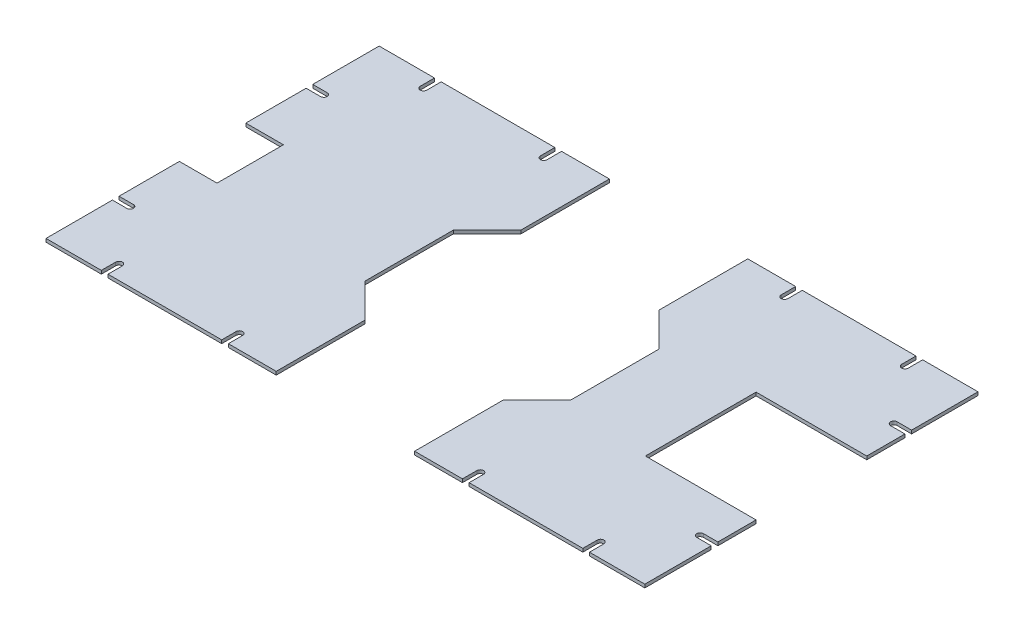
SolidWorks part; units mm, degrees
ref_plane "Front Plane" through (0, 0, 0) normal (0, 0, 1) x (1, 0, 0)
ref_plane "Top Plane" through (0, 0, 0) normal (0, 1, 0) x (1, 0, 0)
ref_plane "Right Plane" through (0, 0, 0) normal (1, 0, 0) x (0, 0, -1)
sketch "Sketch1" plane through (0, 0, 0) normal (0, 1, 0) x (1, 0, 0)
  line L1 (-270.5, -150.5) -> (270.5, -150.5)
  line L2 (-270.5, -150.5) -> (-270.5, 150.5)
  line L3 (-270.5, 150.5) -> (270.5, 150.5)
  line L4 (270.5, -150.5) -> (270.5, 150.5)
  line L5 (-270.5, -150.5) -> (270.5, 150.5) construction
  line L6 (-270.5, 150.5) -> (270.5, -150.5) construction
  point P0 (0, 0)
  dimension "D1" = 301
  dimension "D2" = 541
extrude "Boss-Extrude1" add sketch "Sketch1" along normal blind 3
sketch "Sketch2" plane through (0, 0, 0) normal (0, -1, 0) x (1, 0, 0)
  line L0 (0, 0) -> (-439.178, 0) construction
  line L1 (-236.5, -30) -> (-236.5, 30)
  line L2 (-236.5, 30) -> (-270.5, 30)
  line L3 (-270.5, -150.5) -> (-270.5, 150.5) construction
  line L4 (-236.5, -30) -> (-270.5, -30)
  line L5 (-270.5, -30) -> (-270.5, 30)
  point P9 (-236.5, 0)
  dimension "D1" = 30
  dimension "D2" = 34
extrude "Cut-Extrude1" cut sketch "Sketch2" against normal blind 10 contours L2 L5 L4 L1
sketch "Sketch3" plane through (0, 0, 0) normal (0, -1, 0) x (1, 0, 0)
  line L0 (270.5, 0) -> (126.2632, 0) construction
  line L2 (370.5, -50) -> (170.5, -50)
  line L3 (370.5, -50) -> (370.5, 50)
  line L4 (370.5, 50) -> (170.5, 50)
  line L5 (170.5, -50) -> (170.5, 50)
  line L6 (370.5, -50) -> (170.5, 50) construction
  line L7 (370.5, 50) -> (170.5, -50) construction
  dimension "D1" = 200
  dimension "D2" = 100
extrude "Cut-Extrude2" cut sketch "Sketch3" against normal blind 5
sketch "Sketch4" plane through (0, 3, 0) normal (0, 1, 0) x (1, 0, 0)
  line L0 (270.5, 150.5) -> (-270.5, 150.5) construction
  line L1 (-62.5, -150.5) -> (62.5, -150.5)
  line L2 (-62.5, -150.5) -> (-62.5, 150.5)
  line L3 (-62.5, 150.5) -> (62.5, 150.5)
  line L4 (62.5, -150.5) -> (62.5, 150.5)
  line L5 (-62.5, -150.5) -> (62.5, 150.5) construction
  line L6 (-62.5, 150.5) -> (62.5, -150.5) construction
  point P0 (0, 0)
  dimension "D1" = 125
extrude "Cut-Extrude3" cut sketch "Sketch4" against normal blind 5
sketch "Sketch5" plane through (0, 3, 0) normal (0, 1, 0) x (1, 0, 0)
  line L0 (0, 0) -> (270.5, 0) construction
  line L1 (270.5, 0) -> (0, 0) construction
  line L2 (0, -150.5) -> (0, 150.5) construction
  line L6 (270.5, 50) -> (270.5, 150.5) construction
  line L7 (-220.5, 150.5) -> (-220.5, 137.5)
  line L8 (-62.5, 150.5) -> (-270.5, 150.5) construction
  line L9 (-214.5, 137.5) -> (-214.5, 150.5)
  line L10 (-214.5, 150.5) -> (-220.5, 150.5)
  line L11 (-270.5, 150.5) -> (-270.5, 30) construction
  line L12 (-105.75, 137.5) -> (-105.75, 150.5)
  line L13 (-111.75, 150.5) -> (-111.75, 137.5)
  line L14 (-105.75, 150.5) -> (-111.75, 150.5)
  line L15 (3, 137.5) -> (3, 150.5)
  line L16 (-3, 150.5) -> (-3, 137.5)
  line L17 (3, 150.5) -> (-3, 150.5)
  line L18 (111.75, 137.5) -> (111.75, 150.5)
  line L19 (105.75, 150.5) -> (105.75, 137.5)
  line L20 (111.75, 150.5) -> (105.75, 150.5)
  line L21 (220.5, 137.5) -> (220.5, 150.5)
  line L22 (214.5, 150.5) -> (214.5, 137.5)
  line L23 (220.5, 150.5) -> (214.5, 150.5)
  line L24 (220.5, -150.5) -> (214.5, -150.5)
  line L25 (214.5, -150.5) -> (214.5, -137.5)
  line L26 (220.5, -137.5) -> (220.5, -150.5)
  line L27 (111.75, -150.5) -> (105.75, -150.5)
  line L28 (105.75, -150.5) -> (105.75, -137.5)
  line L29 (111.75, -137.5) -> (111.75, -150.5)
  line L30 (3, -150.5) -> (-3, -150.5)
  line L31 (-3, -150.5) -> (-3, -137.5)
  line L32 (3, -137.5) -> (3, -150.5)
  line L33 (-105.75, -150.5) -> (-111.75, -150.5)
  line L34 (-111.75, -150.5) -> (-111.75, -137.5)
  line L35 (-105.75, -137.5) -> (-105.75, -150.5)
  line L36 (-214.5, -150.5) -> (-220.5, -150.5)
  line L37 (-214.5, -137.5) -> (-214.5, -150.5)
  line L38 (-220.5, -150.5) -> (-220.5, -137.5)
  line L39 (-270.5, 90.5) -> (-257.5, 90.5)
  line L40 (-257.5, 84.5) -> (-270.5, 84.5)
  line L41 (-270.5, 84.5) -> (-270.5, 90.5)
  line L42 (270.5, 84.5) -> (270.5, 90.5)
  line L43 (257.5, 84.5) -> (270.5, 84.5)
  line L44 (270.5, 90.5) -> (257.5, 90.5)
  line L45 (-270.5, 90.5) -> (-257.5, 90.5)
  line L46 (-257.5, 84.5) -> (-270.5, 84.5)
  line L47 (-270.5, 84.5) -> (-270.5, 90.5)
  line L48 (270.5, 84.5) -> (270.5, 90.5)
  line L49 (257.5, 84.5) -> (270.5, 84.5)
  line L50 (270.5, 90.5) -> (257.5, 90.5)
  line L51 (270.5, -90.5) -> (257.5, -90.5)
  line L52 (257.5, -84.5) -> (270.5, -84.5)
  line L53 (270.5, -84.5) -> (270.5, -90.5)
  line L54 (-270.5, -84.5) -> (-270.5, -90.5)
  line L55 (-257.5, -84.5) -> (-270.5, -84.5)
  line L56 (-270.5, -90.5) -> (-257.5, -90.5)
  line L57 (270.5, -90.5) -> (257.5, -90.5)
  line L58 (257.5, -84.5) -> (270.5, -84.5)
  line L59 (270.5, -84.5) -> (270.5, -90.5)
  line L60 (-270.5, -84.5) -> (-270.5, -90.5)
  line L61 (-257.5, -84.5) -> (-270.5, -84.5)
  line L62 (-270.5, -90.5) -> (-257.5, -90.5)
  arc A0 (-220.5, 137.5) -> (-214.5, 137.5) centre (-217.5, 137.5) ccw
  arc A1 (-111.75, 137.5) -> (-105.75, 137.5) centre (-108.75, 137.5) ccw
  arc A2 (-3, 137.5) -> (3, 137.5) centre (0, 137.5) ccw
  arc A3 (105.75, 137.5) -> (111.75, 137.5) centre (108.75, 137.5) ccw
  arc A4 (214.5, 137.5) -> (220.5, 137.5) centre (217.5, 137.5) ccw
  arc A5 (214.5, -137.5) -> (220.5, -137.5) centre (217.5, -137.5) cw
  arc A6 (105.75, -137.5) -> (111.75, -137.5) centre (108.75, -137.5) cw
  arc A7 (-3, -137.5) -> (3, -137.5) centre (0, -137.5) cw
  arc A8 (-111.75, -137.5) -> (-105.75, -137.5) centre (-108.75, -137.5) cw
  arc A9 (-220.5, -137.5) -> (-214.5, -137.5) centre (-217.5, -137.5) cw
  arc A10 (-257.5, 90.5) -> (-257.5, 84.5) centre (-257.5, 87.5) cw
  arc A11 (257.5, 90.5) -> (257.5, 84.5) centre (257.5, 87.5) ccw
  arc A12 (-257.5, 90.5) -> (-257.5, 84.5) centre (-257.5, 87.5) cw
  arc A13 (257.5, 90.5) -> (257.5, 84.5) centre (257.5, 87.5) ccw
  arc A14 (257.5, -90.5) -> (257.5, -84.5) centre (257.5, -87.5) cw
  arc A15 (-257.5, -90.5) -> (-257.5, -84.5) centre (-257.5, -87.5) ccw
  arc A16 (257.5, -90.5) -> (257.5, -84.5) centre (257.5, -87.5) cw
  arc A17 (-257.5, -90.5) -> (-257.5, -84.5) centre (-257.5, -87.5) ccw
  line M8 (-270.5, -150.5) -> (-62.5, -150.5)
  line M10 (-62.5, 150.5) -> (-270.5, 150.5)
  line M11 (-270.5, 150.5) -> (-270.5, 30)
  line M15 (-270.5, -30) -> (-270.5, -150.5)
  dimension "D6" = 3
  dimension "D1" = 50
  dimension "D2" = 6
  dimension "D3" = 13
  dimension "D5" = 13
  dimension "D7" = 60
  dimension "D4" = 5
extrude "Cut-Extrude4" cut sketch "Sketch5" against normal blind 10 contours L56 A15 L55 M15 | A8 L34 L35 M8 | A10 L39 L40 M11 | L7 A0 L9 M10 | L19 A3 L18 L20 | L22 A4 L21 L23 | L44 A11 L43 L42 | A14 L51 L53 L52 | A5 L25 L24 L26 | A6 L28 L27 L29 | L37 L36 L38 A9 | L12 L14 L13 A1
sketch "Sketch6" plane through (0, 3, 0) normal (0, 1, 0) x (1, 0, 0)
  line L0 (0, 0) -> (0, 150.5) construction
  line L1 (62.5, 150.5) -> (-62.5, 150.5)
  line L2 (-62.5, 150.5) -> (-62.5, 70.5)
  line L3 (-62.5, 150.5) -> (-62.5, -150.5) construction
  line L4 (-62.5, 70.5) -> (-93, 40)
  line L5 (-93, 40) -> (-93, -40)
  line L6 (0, 0) -> (-93, 0) construction
  line L7 (-62.5, -70.5) -> (-93, -40)
  line L8 (-62.5, -150.5) -> (-62.5, -70.5)
  line L9 (62.5, -150.5) -> (-62.5, -150.5)
  line L10 (62.5, -150.5) -> (62.5, -70.5)
  line L11 (62.5, -70.5) -> (93, -40)
  line L12 (93, 40) -> (93, -40)
  line L13 (62.5, 70.5) -> (93, 40)
  line L14 (62.5, 150.5) -> (62.5, 70.5)
  point P15 (0, -150.5)
  dimension "D1" = 80
  dimension "D2" = 45
  dimension "D3" = 40
extrude "Cut-Extrude5" cut sketch "Sketch6" against normal blind 10
